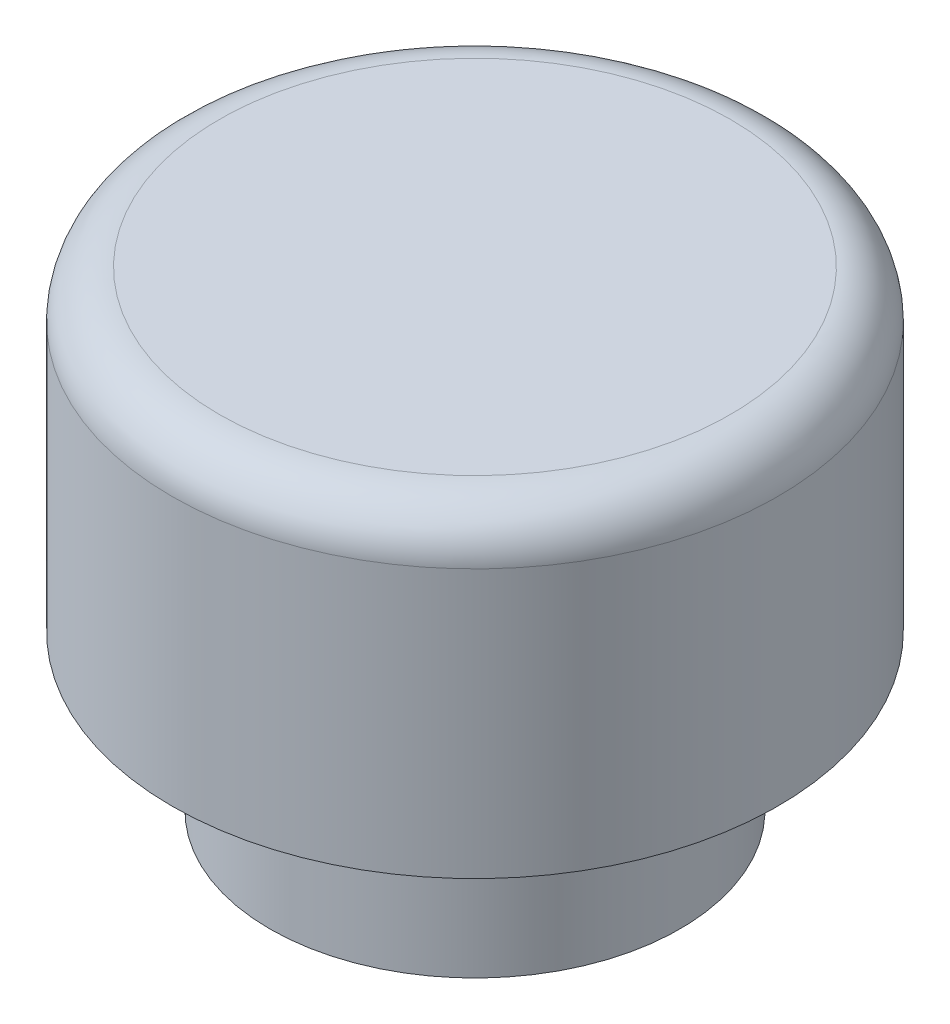
SolidWorks part; units mm, degrees
ref_plane "Front Plane" through (0, 0, 0) normal (0, 0, 1) x (1, 0, 0)
ref_plane "Top Plane" through (0, 0, 0) normal (0, 1, 0) x (1, 0, 0)
ref_plane "Right Plane" through (0, 0, 0) normal (1, 0, 0) x (0, 0, -1)
sketch "Sketch1" plane through (0, 0, 0) normal (0, 1, 0) x (1, 0, 0)
  circle A0 centre (0, 0) radius 3.25
  dimension "D1" = 6.5
extrude "Boss-Extrude1" add sketch "Sketch1" along normal blind 2.46 contours A0
sketch "Sketch2" plane through (0, 0, 0) normal (0, -1, 0) x (1, 0, 0)
  circle A1 centre (0, 0) radius 1.75
  dimension "D1" = 3.5
extrude "Cut-Extrude1" cut sketch "Sketch2" against normal blind 3.35
sketch "Sketch6" plane through (0, 2.46, 0) normal (0, 1, 0) x (1, 0, 0)
  circle A0 centre (0, 0) radius 4.8
  dimension "D1" = 9.6
extrude "Boss-Extrude2" add sketch "Sketch6" along normal blind 5 contours A0
fillet "Fillet1" radius 0.75 1 edges at (0, 7.46, 4.8)
